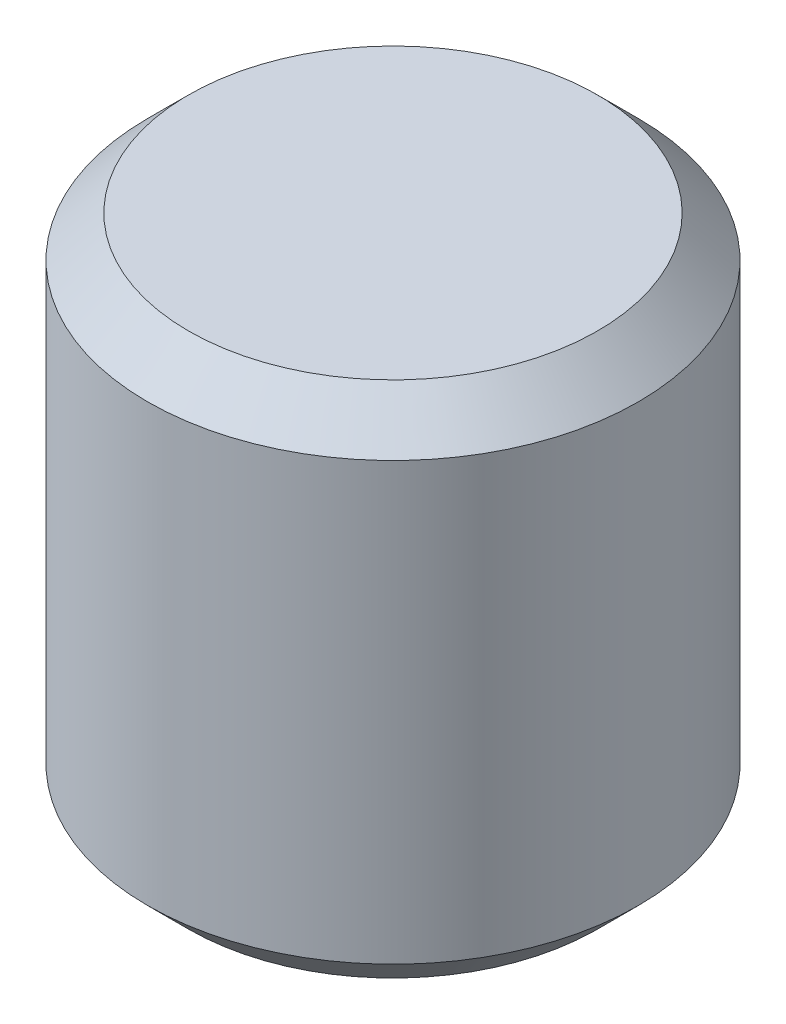
SolidWorks part; units mm, degrees
ref_plane "Front Plane" through (0, 0, 0) normal (0, 0, 1) x (1, 0, 0)
ref_plane "Top Plane" through (0, 0, 0) normal (0, 1, 0) x (1, 0, 0)
ref_plane "Right Plane" through (0, 0, 0) normal (1, 0, 0) x (0, 0, -1)
sketch "Sketch1" plane through (0, 0, 0) normal (0, 1, 0) x (1, 0, 0)
  circle A0 centre (0, 0) radius 9
  dimension "D1" = 18
extrude "Boss-Extrude1" add sketch "Sketch1" along normal blind 19
chamfer "Chamfer1" distance 1.5 angle 45 2 edges at (0, 19, 9) (0, 0, 9)
